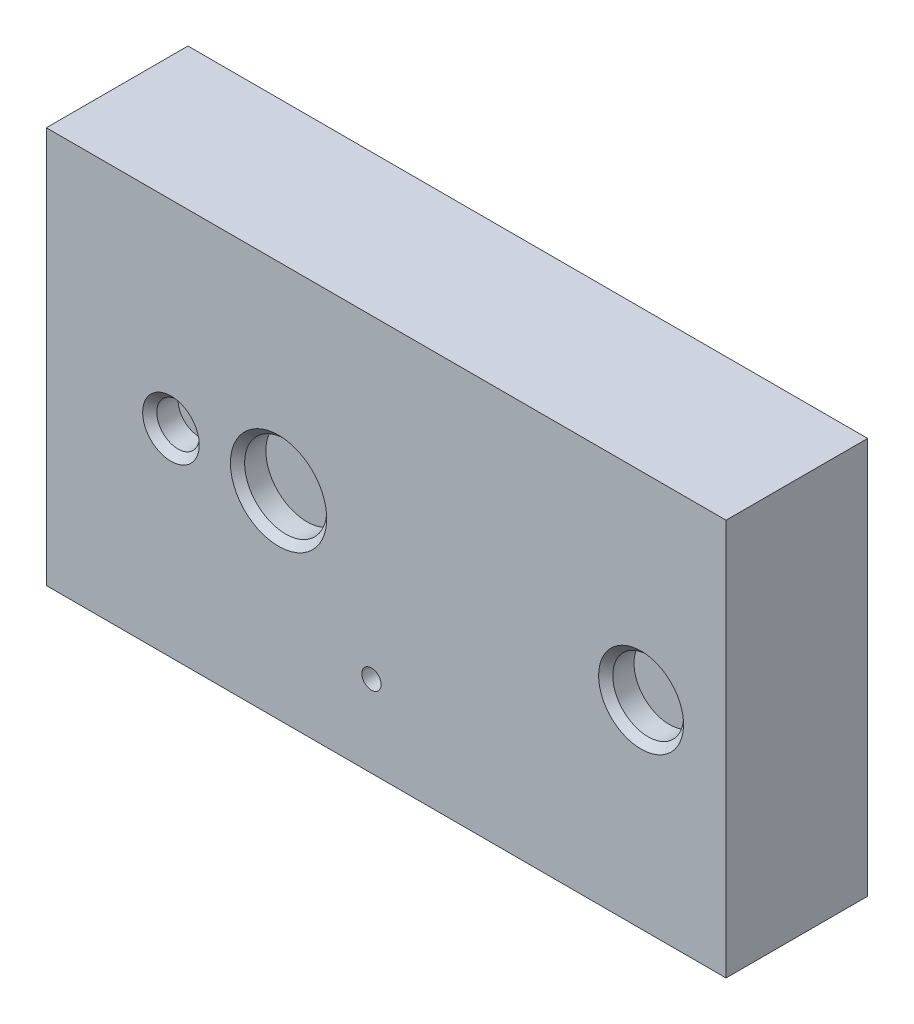
SolidWorks part; units mm, degrees
ref_plane "Front Plane" through (0, 0, 0) normal (0, 0, 1) x (1, 0, 0)
ref_plane "Top Plane" through (0, 0, 0) normal (0, 1, 0) x (1, 0, 0)
ref_plane "Right Plane" through (0, 0, 0) normal (1, 0, 0) x (0, 0, -1)
sketch "Sketch1" plane through (0, 0, 0) normal (0, 0, 1) x (1, 0, 0)
  line L1 (-2.4, -1.4) -> (2.4, -1.4)
  line L2 (-2.4, -1.4) -> (-2.4, 1.4)
  line L3 (-2.4, 1.4) -> (2.4, 1.4)
  line L4 (2.4, -1.4) -> (2.4, 1.4)
  line L5 (-2.4, -1.4) -> (2.4, 1.4) construction
  line L6 (-2.4, 1.4) -> (2.4, -1.4) construction
  point P0 (0, 0)
  dimension "D1" = 2.8
  dimension "D2" = 4.8
extrude "Boss-Extrude1" add sketch "Sketch1" along normal blind 1
sketch "Sketch2" plane through (0, 0, 1) normal (0, 0, 1) x (1, 0, 0)
  line L1 (2.4, -1.4) -> (2.4, 1.4) construction
  line L2 (-3.5157, 0) -> (4.0106, 0) construction
  circle A0 centre (1.8, 0) radius 0.25
  circle A1 centre (-0.104, -0.8239) radius 0.0681
  circle A2 centre (-0.76, 0) radius 0.29
  circle A3 centre (-1.52, 0) radius 0.15
  point P12 (2.4, 0)
  dimension "D1" = 0.5
  dimension "D2" = 0.58
  dimension "D6" = 0.3
  dimension "D3" = 2.56
  dimension "D4" = 0.6
  dimension "D5" = 3.32
extrude "Cut-Extrude1" cut sketch "Sketch2" against normal blind 0.2
chamfer "Chamfer1" distance 0.05 angle 45 3 edges at (2.05, 0, 1) (-1.37, 0, 1) (-0.47, 0, 1)
sketch "Sketch3" plane through (0, 0, 0) normal (0, 0, -1) x (-1, 0, 0)
  line L1 (2.15, -1.3) -> (1.6, -1.3)
  line L2 (2.15, -1.3) -> (2.15, -0.7)
  line L3 (2.15, -0.7) -> (1.6, -0.7)
  line L4 (1.6, -1.3) -> (1.6, -0.7)
  line L5 (2.4, 1.4) -> (2.4, -1.4) construction
  line L6 (2.4, -1.4) -> (-2.4, -1.4) construction
  line L7 (1.4, -0.7) -> (0.85, -0.7)
  line L8 (1.4, -1.3) -> (1.4, -0.7)
  line L9 (1.4, -1.3) -> (0.85, -1.3)
  line L10 (0.85, -1.3) -> (0.85, -0.7)
  line L11 (0.65, -0.7) -> (0.1, -0.7)
  line L12 (0.65, -1.3) -> (0.65, -0.7)
  line L13 (0.65, -1.3) -> (0.1, -1.3)
  line L14 (0.1, -1.3) -> (0.1, -0.7)
  line L15 (-0.1, -0.7) -> (-0.65, -0.7)
  line L16 (-0.1, -1.3) -> (-0.1, -0.7)
  line L17 (-0.1, -1.3) -> (-0.65, -1.3)
  line L18 (-0.65, -1.3) -> (-0.65, -0.7)
  line L19 (-0.85, -0.7) -> (-1.4, -0.7)
  line L20 (-0.85, -1.3) -> (-0.85, -0.7)
  line L21 (-0.85, -1.3) -> (-1.4, -1.3)
  line L22 (-1.4, -1.3) -> (-1.4, -0.7)
  line L23 (-1.6, -0.7) -> (-2.15, -0.7)
  line L24 (-1.6, -1.3) -> (-1.6, -0.7)
  line L25 (-1.6, -1.3) -> (-2.15, -1.3)
  line L26 (-2.15, -1.3) -> (-2.15, -0.7)
  line L27 (1.4, 1.3) -> (0.85, 1.3)
  line L28 (1.4, 0.7) -> (1.4, 1.3)
  line L29 (1.4, 0.7) -> (0.85, 0.7)
  line L30 (0.85, 0.7) -> (0.85, 1.3)
  line L31 (0.65, 1.3) -> (0.1, 1.3)
  line L32 (0.65, 0.7) -> (0.65, 1.3)
  line L33 (0.65, 0.7) -> (0.1, 0.7)
  line L34 (0.1, 0.7) -> (0.1, 1.3)
  line L35 (-0.1, 1.3) -> (-0.65, 1.3)
  line L36 (-0.1, 0.7) -> (-0.1, 1.3)
  line L37 (-0.1, 0.7) -> (-0.65, 0.7)
  line L38 (-0.65, 0.7) -> (-0.65, 1.3)
  line L39 (-0.85, 1.3) -> (-1.4, 1.3)
  line L40 (-0.85, 0.7) -> (-0.85, 1.3)
  line L41 (-0.85, 0.7) -> (-1.4, 0.7)
  line L42 (-1.4, 0.7) -> (-1.4, 1.3)
  line L43 (-1.6, 1.3) -> (-2.15, 1.3)
  line L44 (-1.6, 0.7) -> (-1.6, 1.3)
  line L45 (-1.6, 0.7) -> (-2.15, 0.7)
  line L46 (-2.15, 0.7) -> (-2.15, 1.3)
  line L47 (2.15, 1.3) -> (1.6, 1.3)
  line L48 (2.15, 0.7) -> (2.15, 1.3)
  line L49 (2.15, 0.7) -> (1.6, 0.7)
  line L50 (1.6, 0.7) -> (1.6, 1.3)
  dimension "D1" = 0.25
  dimension "D2" = 0.55
  dimension "D3" = 0.6
  dimension "D4" = 0.1
  dimension "D5" = 6
  dimension "D6" = 2
extrude "Cut-Extrude2" cut sketch "Sketch3" against normal blind 0.001
